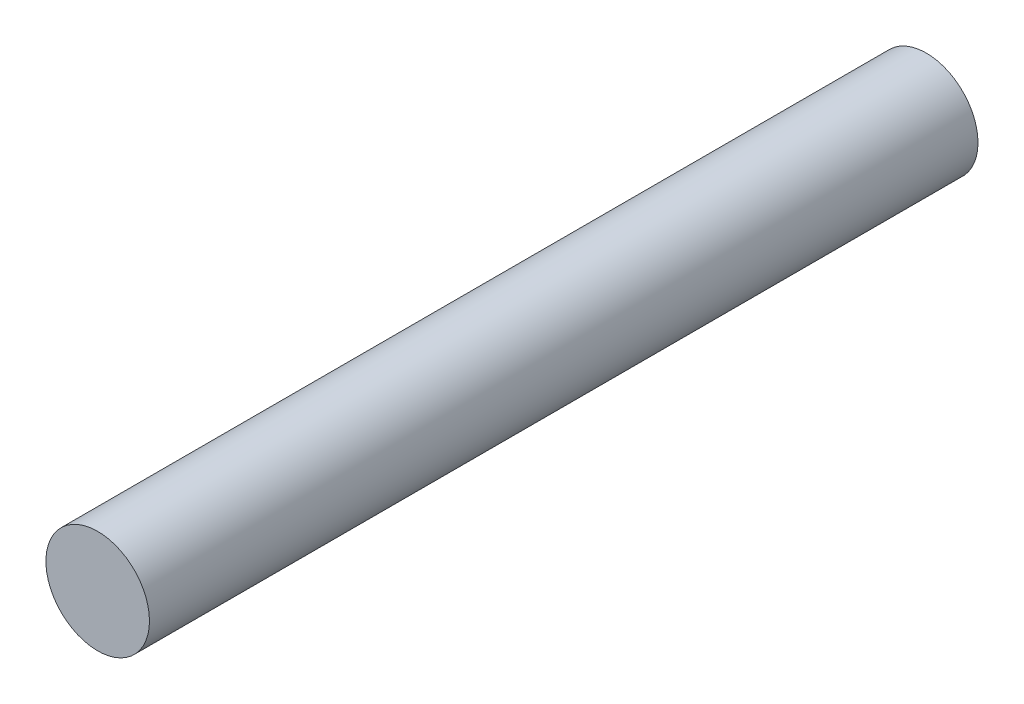
SolidWorks part; units mm, degrees
ref_plane "Front Plane" through (0, 0, 0) normal (0, 0, 1) x (1, 0, 0)
ref_plane "Top Plane" through (0, 0, 0) normal (0, 1, 0) x (1, 0, 0)
ref_plane "Right Plane" through (0, 0, 0) normal (1, 0, 0) x (0, 0, -1)
sketch "Sketch1" plane through (0, 0, 0) normal (0, 0, 1) x (1, 0, 0)
  circle A0 centre (0, 0) radius 12.5
extrude "Boss-Extrude1" add sketch "Sketch1" along normal blind 200
